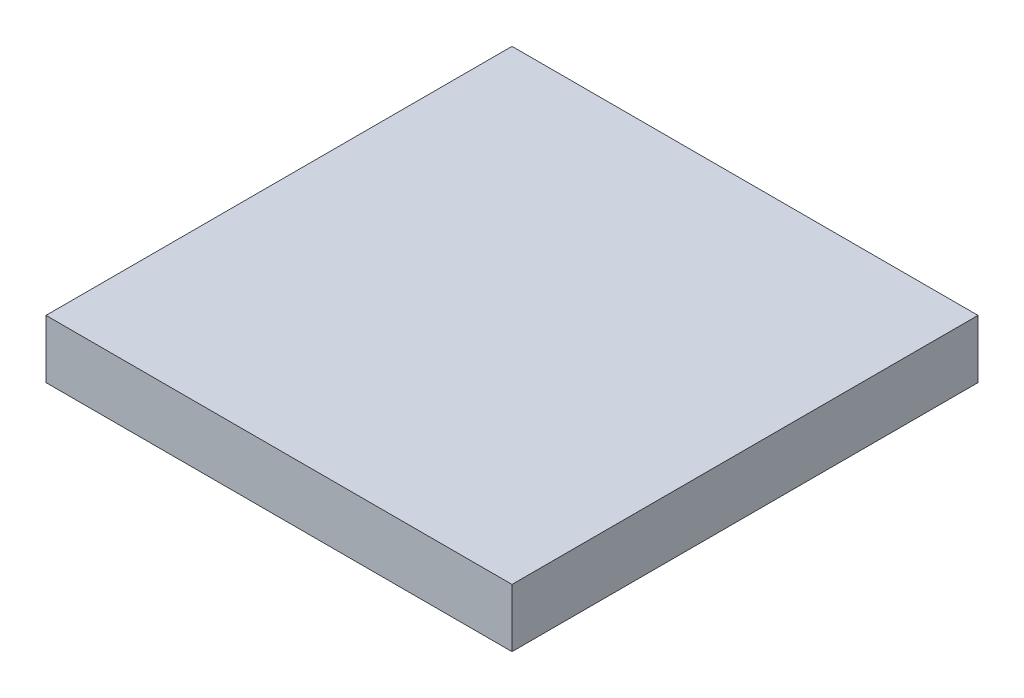
SolidWorks part; units mm, degrees
material "Custom Plastic"
ref_plane "Front Plane" through (0, 0, 0) normal (0, 0, 1) x (1, 0, 0)
ref_plane "Top Plane" through (0, 0, 0) normal (0, 1, 0) x (1, 0, 0)
ref_plane "Right Plane" through (0, 0, 0) normal (1, 0, 0) x (0, 0, -1)
sketch "Sketch1" plane through (0, 0, 0) normal (0, 1, 0) x (1, 0, 0)
  line L1 (-10.16, 10.16) -> (10.16, 10.16)
  line L2 (-10.16, 10.16) -> (-10.16, -10.16)
  line L3 (-10.16, -10.16) -> (10.16, -10.16)
  line L4 (10.16, 10.16) -> (10.16, -10.16)
  line L5 (-10.16, 10.16) -> (10.16, -10.16) construction
  line L6 (-10.16, -10.16) -> (10.16, 10.16) construction
  point P0 (0, 0)
extrude "Extrude1" add sketch "Sketch1" along normal blind 2.54
